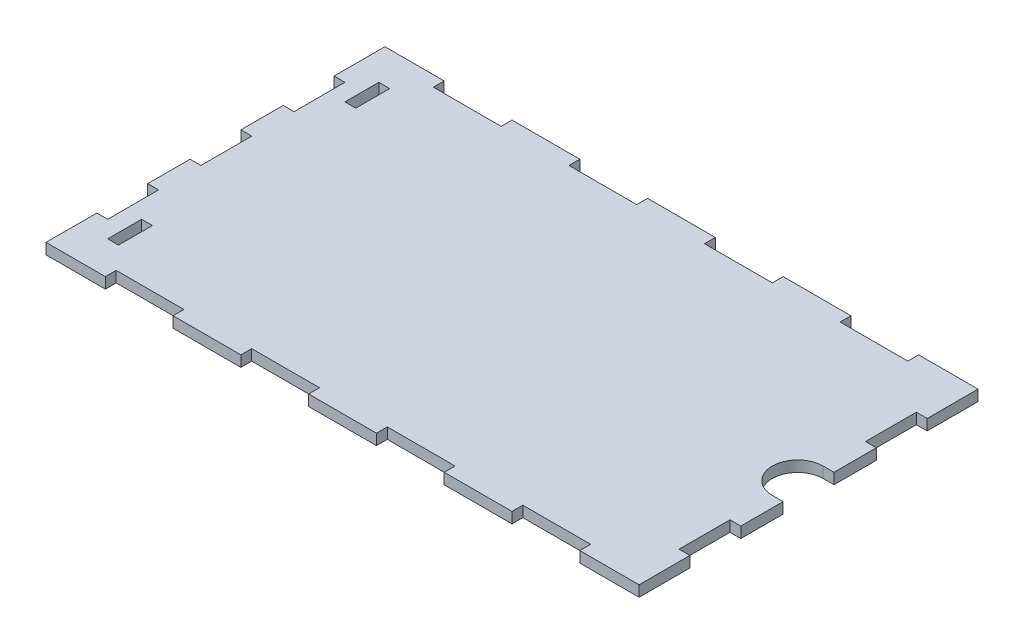
SolidWorks part; units mm, degrees
ref_plane "Front Plane" through (0, 0, 0) normal (0, 0, 1) x (1, 0, 0)
ref_plane "Top Plane" through (0, 0, 0) normal (0, 1, 0) x (1, 0, 0)
ref_plane "Right Plane" through (0, 0, 0) normal (1, 0, 0) x (0, 0, -1)
sketch "Sketch1" plane through (0, 0, 0) normal (0, 1, 0) x (1, 0, 0)
  line L0 (-87.5, 7.5) -> (-87.5, 20)
  line L1 (-55, 0) -> (55, 0) construction
  line L2 (-87.5, 50) -> (-70, 50)
  line L3 (0, -55) -> (0, 55) construction
  line L4 (-87.5, 35) -> (-84.3, 35)
  line L5 (-84.3, 35) -> (-84.3, 20)
  line L6 (-84.3, 20) -> (-87.5, 20)
  line L7 (-87.5, 7.5) -> (-84.3, 7.5)
  line L8 (-84.3, 7.5) -> (-84.3, -7.5)
  line L9 (-87.5, 35) -> (-87.5, 50)
  line L10 (-70, 50) -> (-70, 46.8)
  line L11 (-70, 46.8) -> (-50, 46.8)
  line L12 (-50, 46.8) -> (-50, 50)
  line L13 (-30, 50) -> (-30, 46.8)
  line L14 (-30, 46.8) -> (-10, 46.8)
  line L15 (-10, 46.8) -> (-10, 50)
  line L16 (0, 50) -> (0, 0) construction
  line L17 (0, 0) -> (-84.3, 0) construction
  line L18 (-50, 50) -> (-30, 50)
  line L19 (-10, 50) -> (10, 50)
  line L20 (-10, -50) -> (10, -50)
  line L21 (-50, -50) -> (-30, -50)
  line L22 (-10, -46.8) -> (-10, -50)
  line L23 (-30, -46.8) -> (-10, -46.8)
  line L24 (-30, -50) -> (-30, -46.8)
  line L25 (-50, -46.8) -> (-50, -50)
  line L26 (-70, -46.8) -> (-50, -46.8)
  line L27 (-70, -50) -> (-70, -46.8)
  line L28 (-87.5, -35) -> (-87.5, -50)
  line L29 (-87.5, -7.5) -> (-84.3, -7.5)
  line L30 (-84.3, -20) -> (-87.5, -20)
  line L31 (-84.3, -35) -> (-84.3, -20)
  line L32 (-87.5, -35) -> (-84.3, -35)
  line L33 (-87.5, -50) -> (-70, -50)
  line L34 (-87.5, -7.5) -> (-87.5, -20)
  line L35 (87.5, -7.5) -> (87.5, -20)
  line L36 (87.5, -50) -> (70, -50)
  line L37 (87.5, -35) -> (84.3, -35)
  line L38 (84.3, -35) -> (84.3, -20)
  line L39 (84.3, -20) -> (87.5, -20)
  line L40 (87.5, -7.5) -> (84.3, -7.5)
  line L41 (87.5, -35) -> (87.5, -50)
  line L42 (70, -50) -> (70, -46.8)
  line L43 (70, -46.8) -> (50, -46.8)
  line L44 (50, -46.8) -> (50, -50)
  line L45 (30, -50) -> (30, -46.8)
  line L46 (30, -46.8) -> (10, -46.8)
  line L47 (10, -46.8) -> (10, -50)
  line L48 (50, -50) -> (30, -50)
  line L49 (50, 50) -> (30, 50)
  line L50 (10, 46.8) -> (10, 50)
  line L51 (30, 46.8) -> (10, 46.8)
  line L52 (30, 50) -> (30, 46.8)
  line L53 (50, 46.8) -> (50, 50)
  line L54 (70, 46.8) -> (50, 46.8)
  line L55 (70, 50) -> (70, 46.8)
  line L56 (87.5, 35) -> (87.5, 50)
  line L57 (-76.1, 40) -> (-76.1, 30)
  line L58 (87.5, 7.5) -> (84.3, 7.5)
  line L59 (84.3, 20) -> (87.5, 20)
  line L60 (84.3, 35) -> (84.3, 20)
  line L61 (87.5, 35) -> (84.3, 35)
  line L62 (87.5, 50) -> (70, 50)
  line L63 (87.5, 7.5) -> (87.5, 20)
  line L64 (-79.3, -40) -> (-76.1, -40)
  line L65 (-79.3, -40) -> (-79.3, -30)
  line L66 (-79.3, -30) -> (-76.1, -30)
  line L67 (-76.1, -40) -> (-76.1, -30)
  line L68 (-79.3, 30) -> (-76.1, 30)
  line L69 (-79.3, 40) -> (-79.3, 30)
  line L70 (-79.3, 40) -> (-76.1, 40)
  arc A0 (84.3, 7.5) -> (84.3, -7.5) centre (84.3, 0) ccw
  point P40 (0, -50)
  dimension "D1" = 50
  dimension "D2" = 87.5
  dimension "D3" = 15
  dimension "D4" = 15
  dimension "D5" = 7.5
  dimension "D6" = 3.2
  dimension "D7" = 20
  dimension "D8" = 20
  dimension "D9" = 20
  dimension "D10" = 10
  dimension "D11" = 3.2
  dimension "D12" = 10
  dimension "D13" = 5
  dimension "D14" = 10
extrude "Boss-Extrude1" add sketch "Sketch1" along normal blind 3.2
